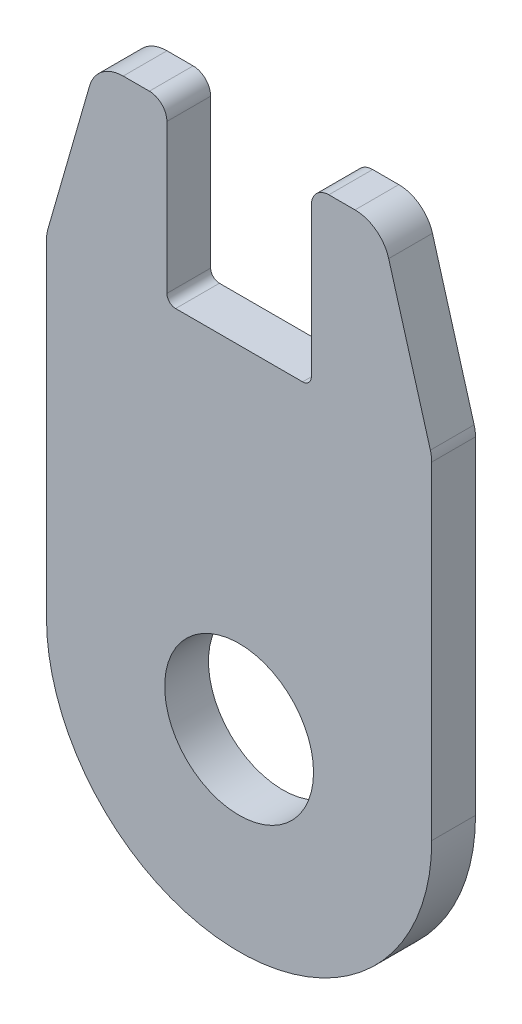
SolidWorks part; units mm, degrees
ref_plane "Plane1" through (0, 0, 0) normal (0, 0, 1) x (1, 0, 0)
ref_plane "Plane2" through (0, 0, 0) normal (0, 1, 0) x (1, 0, 0)
ref_plane "Plane3" through (0, 0, 0) normal (1, 0, 0) x (0, 0, -1)
sketch "Sketch1" plane through (0, 0, 0) normal (0, 0, 1) x (1, 0, 0)
  line L0 (11, 0) -> (11, 18.7182)
  line L1 (6.619, 29) -> (5.125, 29)
  line L2 (4.125, 28) -> (4.125, 19.5)
  line L3 (3.625, 19) -> (-3.625, 19)
  line L4 (0, 0) -> (0, 89.8787) construction
  line L5 (-11, 0) -> (-11, 18.7182)
  line L6 (-6.619, 29) -> (-5.125, 29)
  line L7 (-4.125, 28) -> (-4.125, 19.5)
  line L8 (8.5411, 27.5526) -> (10.9221, 19.2708)
  line L9 (-8.5411, 27.5526) -> (-10.9221, 19.2708)
  circle A0 centre (0, 0) radius 4.25
  arc A1 (11, 0) -> (-11, 0) centre (0, 0) cw
  arc A2 (8.5411, 27.5526) -> (6.619, 29) centre (6.619, 27) ccw
  arc A3 (10.9221, 19.2708) -> (11, 18.7182) centre (9, 18.7182) cw
  arc A4 (-8.5411, 27.5526) -> (-6.619, 29) centre (-6.619, 27) cw
  arc A5 (-10.9221, 19.2708) -> (-11, 18.7182) centre (-9, 18.7182) ccw
  arc A6 (5.125, 29) -> (4.125, 28) centre (5.125, 28) ccw
  arc A7 (-5.125, 29) -> (-4.125, 28) centre (-5.125, 28) cw
  arc A8 (4.125, 19.5) -> (3.625, 19) centre (3.625, 19.5) cw
  arc A9 (-4.125, 19.5) -> (-3.625, 19) centre (-3.625, 19.5) ccw
  point P16 (0, 19)
  point P19 (8.125, 29)
  point P22 (11, 19)
  point P25 (-8.125, 29)
  point P28 (-11, 19)
  point P31 (4.125, 29)
  point P34 (-4.125, 29)
  point P37 (4.125, 19)
  point P40 (-4.125, 19)
  dimension "D2" = 8.5
  dimension "D8" = 2
  dimension "D9" = 1
  dimension "D10" = 0.5
  dimension "D1" = 8.25
  dimension "D3" = 22
  dimension "D4" = 10
  dimension "D5" = 29
  dimension "D6" = 4
  dimension "D7" = 10
extrude "Extrude1" add sketch "Sketch1" along normal mid plane 2.5
